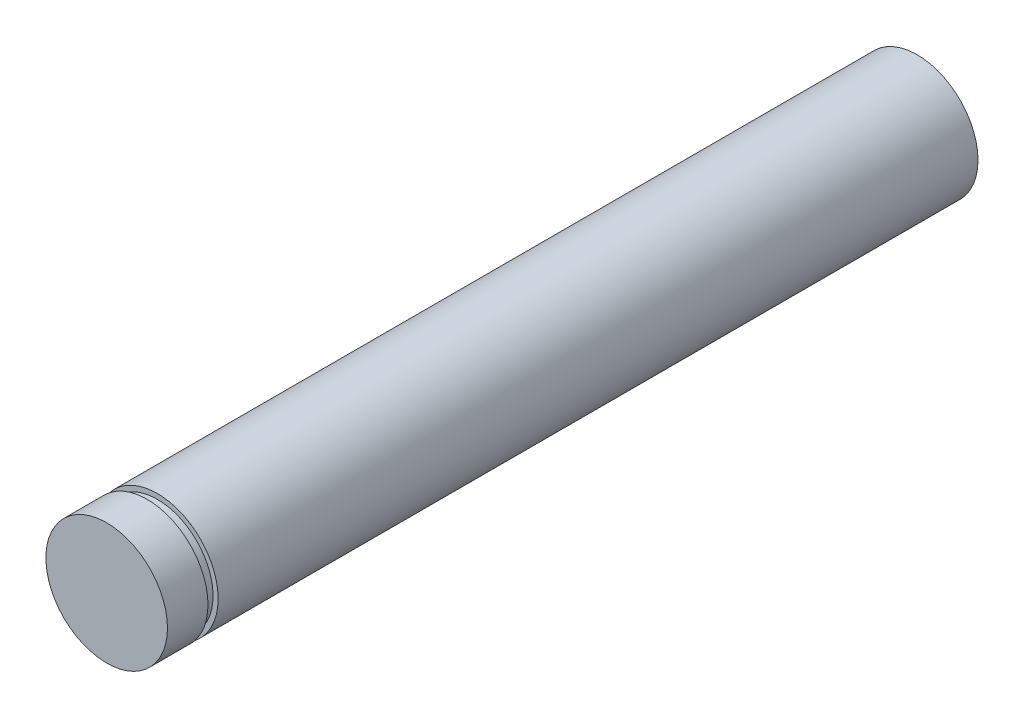
SolidWorks part; units mm, degrees
ref_plane "前视基准面" through (0, 0, 0) normal (0, 0, 1) x (1, 0, 0)
ref_plane "上视基准面" through (0, 0, 0) normal (0, 1, 0) x (1, 0, 0)
ref_plane "右视基准面" through (0, 0, 0) normal (1, 0, 0) x (0, 0, -1)
sketch "草图1" plane through (0, 0, 0) normal (0, 0, 1) x (1, 0, 0)
  circle A0 centre (0, 0) radius 6
extrude "凸台-拉伸1" add sketch "草图1" along normal blind 70 and the other way blind 10
ref_plane "基准面1" through (0, 0, 0) normal (0, 0, -1) x (-1, 0, 0)
sketch "草图3" plane through (0, 0, 0) normal (1, 0, 0) x (0, 0, -1)
  line L0 (-70, 0) -> (-65.6055, 0) construction
  line L2 (-66, 5.5) -> (-65, 5.5)
  line L4 (-66, 5.5) -> (-66, 6)
  line L5 (-66, 6) -> (-65, 6)
  line L6 (-65, 6) -> (-65, 5.5)
revolve "切除-旋转1" cut sketch "草图3" angle 360 about L0
